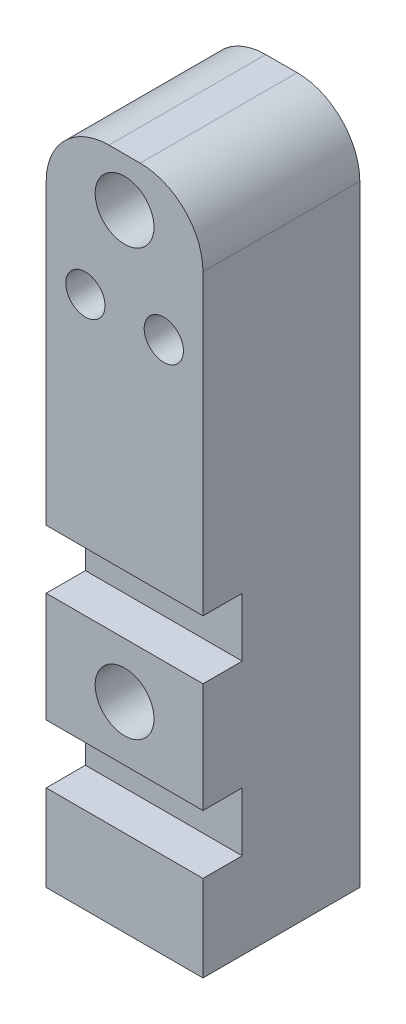
SolidWorks part; units mm, degrees
ref_plane "Front Plane" through (0, 0, 0) normal (0, 0, 1) x (1, 0, 0)
ref_plane "Top Plane" through (0, 0, 0) normal (0, 1, 0) x (1, 0, 0)
ref_plane "Right Plane" through (0, 0, 0) normal (1, 0, 0) x (0, 0, -1)
sketch "Sketch2" plane through (0, 0, 0) normal (0, 0, 1) x (1, 0, 0)
  line L1 (-12.7, -54.61) -> (12.7, -54.61)
  line L2 (-12.7, -54.61) -> (-12.7, 54.61)
  line L3 (-12.7, 54.61) -> (12.7, 54.61)
  line L4 (12.7, -54.61) -> (12.7, 54.61)
  point P0 (0, 0)
  dimension "D1" = 109.22
  dimension "D2" = 25.4
extrude "Boss-Extrude1" add sketch "Sketch2" along normal blind 25.4
sketch "Sketch3" plane through (0, 0, 25.4) normal (0, 0, 1) x (1, 0, 0)
  circle A0 centre (0, -22.225) radius 4.7625
  circle A1 centre (6.35, 31.75) radius 3.175
  circle A2 centre (-6.35, 31.75) radius 3.175
  point P11 (0, 31.75)
extrude "Cut-Extrude1" cut sketch "Sketch3" against normal blind 25.4 contours A2 | A1 | A0
sketch "Sketch4" plane through (0, 0, 25.4) normal (0, 0, 1) x (1, 0, 0)
  line L0 (-12.7, -13.335) -> (12.7, -13.335)
  line L1 (-12.7, -31.115) -> (-12.7, -40.64)
  line L2 (-12.7, -3.81) -> (12.7, -3.81)
  line L3 (12.7, -54.61) -> (12.7, 54.61) construction
  line L4 (12.7, -3.81) -> (12.7, -13.335)
  line L6 (-12.7, 54.61) -> (-12.7, -54.61) construction
  line L7 (-12.7, -13.335) -> (-12.7, -3.81)
  line L9 (-12.7, -40.64) -> (12.7, -40.64)
  line L10 (12.7, -40.64) -> (12.7, -31.115)
  line L11 (-12.7, -31.115) -> (12.7, -31.115)
  point P10 (0, -3.81)
extrude "Cut-Extrude2" cut sketch "Sketch4" against normal blind 6.35
sketch "Sketch5" plane through (0, 0, 25.4) normal (0, 0, 1) x (1, 0, 0)
  circle A0 centre (0, 46.736) radius 4.7625
  dimension "D1" = 9.525
extrude "Cut-Extrude3" cut sketch "Sketch5" against normal blind 16.51
sketch "Sketch6" plane through (0, -54.61, 0) normal (0, -1, 0) x (1, 0, 0)
  circle A0 centre (0, 12.7) radius 2.54
extrude "Cut-Extrude4" cut sketch "Sketch6" against normal blind 17.78
fillet "Fillet1" radius 10.16 2 edges at (-12.7, 54.61, 12.7) (12.7, 54.61, 12.7)
